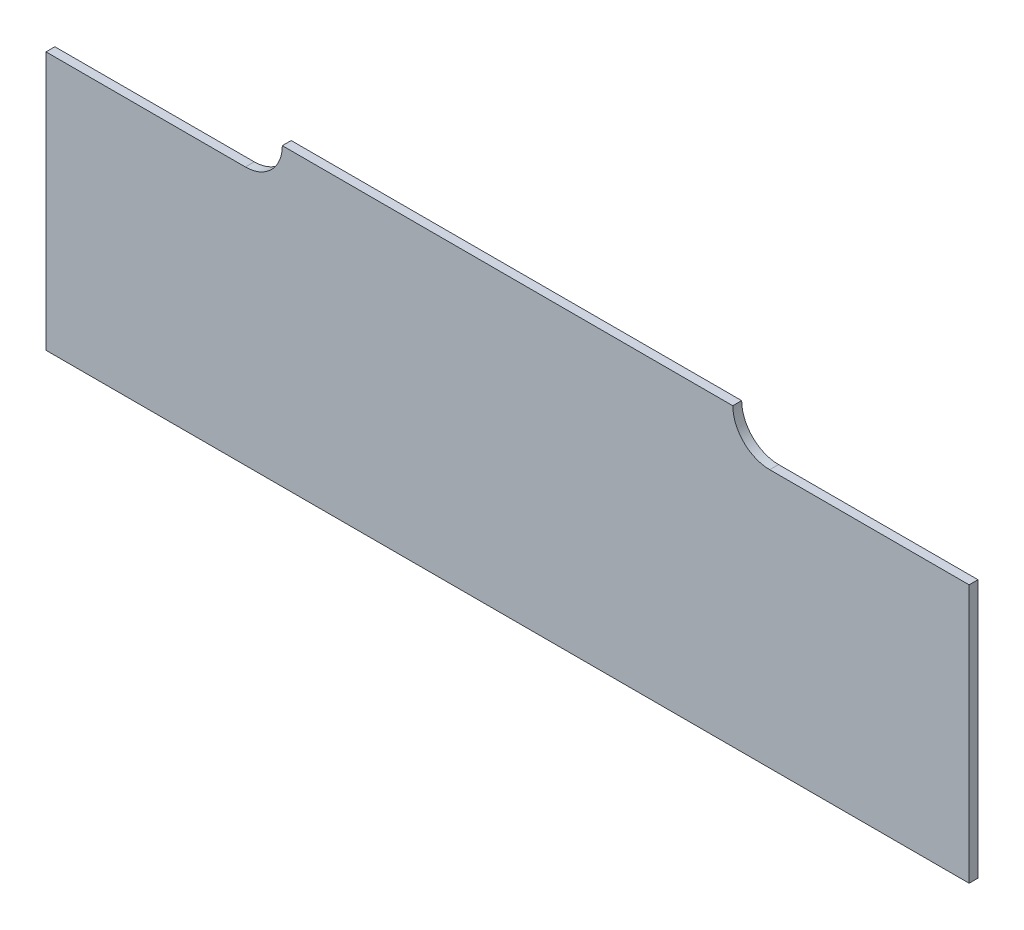
SolidWorks part; units mm, degrees
ref_plane "Ön Düzlem" through (0, 0, 0) normal (0, 0, 1) x (1, 0, 0)
ref_plane "Üst Düzlem" through (0, 0, 0) normal (0, 1, 0) x (1, 0, 0)
ref_plane "Sağ Düzlem" through (0, 0, 0) normal (1, 0, 0) x (0, 0, -1)
ref_plane "Plane1" through (0, 0, 0.12) normal (0, 0, 1) x (1, 0, 0)
sketch "Sketch1" plane through (0, 0, 0.12) normal (0, 0, 1) x (1, 0, 0)
  line L6 (0, 3.5) -> (0, 0)
  line L7 (0, 0) -> (12.5, 0)
  line L8 (12.5, 0) -> (12.5, 3.5)
  line L9 (12.5, 3.5) -> (0, 3.5)
  line L10 (3.2, 4) -> (9.3, 4)
  arc A0 (3.2, 4) -> (2.7, 3.5) centre (2.7, 4) cw
  arc A1 (9.8, 3.5) -> (9.3, 4) centre (9.8, 4) cw
  point P7 (6.25, 4)
  point P8 (6.25, 3.5)
  dimension "D3" = 0.5
  dimension "D1" = 3.5
  dimension "D2" = 12.5
  dimension "D5" = 6.1
extrude "Boss-Extrude1" add sketch "Sketch1" against normal blind 0.12 contours L8 L9 L6 L7 | L9 A1 L10 A0
